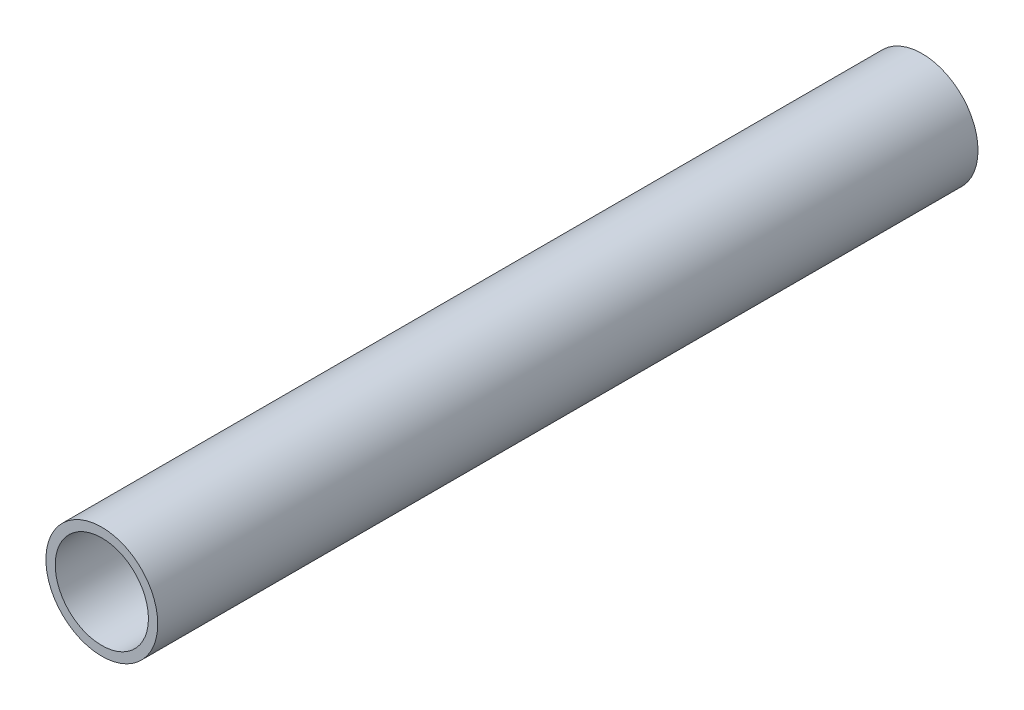
SolidWorks part; units mm, degrees
ref_plane "Front" through (0, 0, 0) normal (0, 0, 1) x (1, 0, 0)
ref_plane "Top" through (0, 0, 0) normal (0, 1, 0) x (1, 0, 0)
ref_plane "Right" through (0, 0, 0) normal (1, 0, 0) x (0, 0, -1)
sketch "Sketch2" plane through (0, 0, 0) normal (0, 0, 1) x (1, 0, 0)
  circle A0 centre (0, 0) radius 15.875
  circle A1 centre (0, 0) radius 19.05
  dimension "D1" = 3.175
  dimension "D2" = 38.1
extrude "Extrude1" add sketch "Sketch2" along normal blind 279.4
